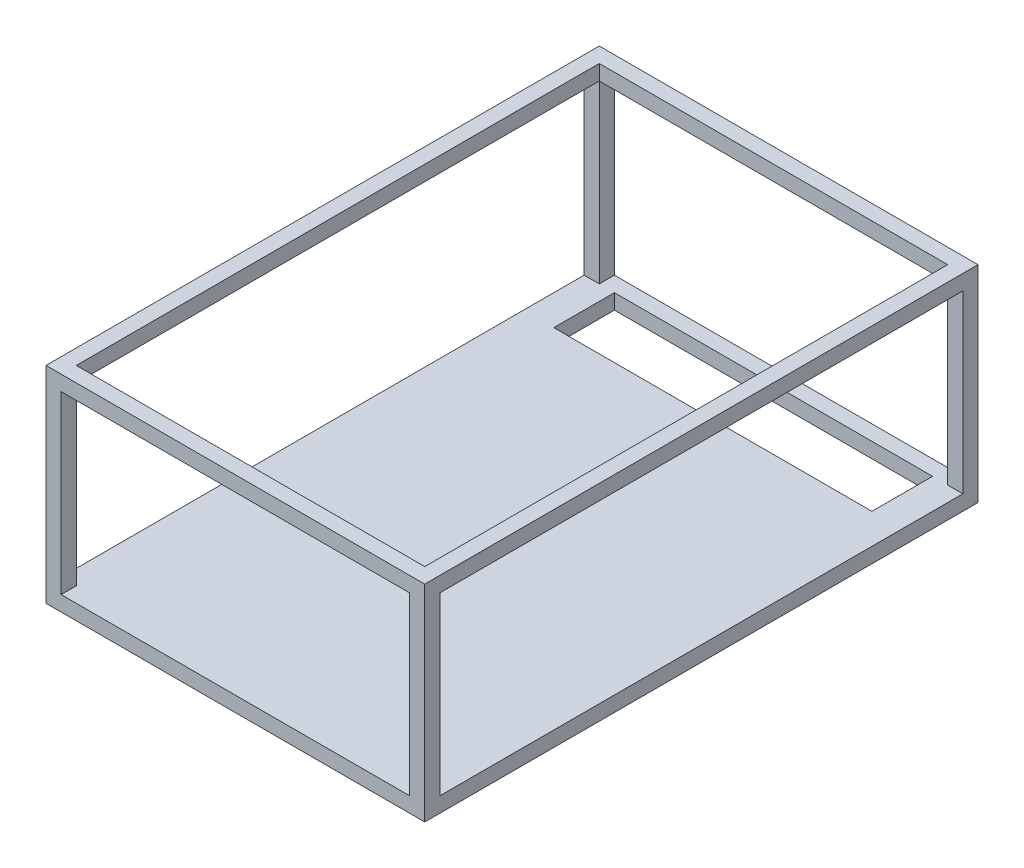
SolidWorks part; units mm, degrees
ref_plane "Ebene vorne" through (0, 0, 0) normal (0, 0, 1) x (1, 0, 0)
ref_plane "Ebene oben" through (0, 0, 0) normal (0, 1, 0) x (1, 0, 0)
ref_plane "Ebene rechts" through (0, 0, 0) normal (1, 0, 0) x (0, 0, -1)
sketch "Sketch1" plane through (0, 0, 0) normal (0, 0, 1) x (1, 0, 0)
  line L1 (-62.5, -34) -> (62.5, -34)
  line L2 (-62.5, -34) -> (-62.5, 34)
  line L3 (-62.5, 34) -> (62.5, 34)
  line L4 (62.5, -34) -> (62.5, 34)
  line L5 (-62.5, -34) -> (62.5, 34) construction
  line L6 (-62.5, 34) -> (62.5, -34) construction
  point P0 (0, 0)
  dimension "D1" = 125
  dimension "D2" = 68
extrude "Boss-Extrude1" add sketch "Sketch1" along normal blind 182.6
sketch "Sketch2" plane through (62.5, 0, 0) normal (1, 0, 0) x (0, 0, -1)
  line L0 (-182.6, 34) -> (0, -34) construction
  line L1 (-182.6, 34) -> (0, 34) construction
  line L2 (-5, -29) -> (-177.6, -29)
  line L3 (-5, -29) -> (-5, 29)
  line L4 (-5, 29) -> (-177.6, 29)
  line L5 (-177.6, -29) -> (-177.6, 29)
  line L6 (-5, -29) -> (-177.6, 29) construction
  line L7 (-5, 29) -> (-177.6, -29) construction
  line L8 (-182.6, -34) -> (-182.6, 34) construction
  point P4 (-91.3, 0)
  dimension "D1" = 5
  dimension "D2" = 5
extrude "Cut-Extrude1" cut sketch "Sketch2" against normal through all
sketch "Sketch3" plane through (0, 0, 0) normal (0, 0, -1) x (-1, 0, 0)
  line L0 (-62.5, 34) -> (62.5, 34) construction
  line L1 (57.5, -29) -> (-57.5, -29)
  line L2 (57.5, -29) -> (57.5, 29)
  line L3 (57.5, 29) -> (-57.5, 29)
  line L4 (-57.5, -29) -> (-57.5, 29)
  line L5 (57.5, -29) -> (-57.5, 29) construction
  line L6 (57.5, 29) -> (-57.5, -29) construction
  line L7 (-62.5, -34) -> (-62.5, 34) construction
  point P0 (0, 0)
  dimension "D1" = 5
  dimension "D2" = 5
extrude "Cut-Extrude2" cut sketch "Sketch3" against normal through all
sketch "Sketch4" plane through (0, 34, 0) normal (0, 1, 0) x (1, 0, 0)
  line L0 (-62.5, 0) -> (62.5, -182.6) construction
  line L1 (62.5, -182.6) -> (62.5, 0) construction
  line L2 (-57.5, -5) -> (57.5, -5)
  line L3 (-57.5, -5) -> (-57.5, -177.6)
  line L4 (-57.5, -177.6) -> (57.5, -177.6)
  line L5 (57.5, -5) -> (57.5, -177.6)
  line L6 (-57.5, -5) -> (57.5, -177.6) construction
  line L7 (-57.5, -177.6) -> (57.5, -5) construction
  line L8 (62.5, 0) -> (-62.5, 0) construction
  point P4 (0, -91.3)
  dimension "D1" = 5
  dimension "D2" = 5
extrude "Cut-Extrude3" cut sketch "Sketch4" against normal blind 63
sketch "Sketch5" plane through (0, -29, 0) normal (0, 1, 0) x (1, 0, 0)
  line L0 (-62.5, -15) -> (62.5, -15) construction
  line L1 (-62.5, -182.6) -> (-62.5, 0) construction
  line L2 (62.5, -182.6) -> (62.5, 0) construction
  line L4 (57.5, -5) -> (-57.5, -5) construction
  line L5 (57.5, -177.6) -> (57.5, -5) construction
  line L6 (-52.5, -25) -> (52.5, -25)
  line L7 (-52.5, -25) -> (-52.5, -5)
  line L8 (-52.5, -5) -> (52.5, -5)
  line L9 (52.5, -25) -> (52.5, -5)
  line L10 (-52.5, -25) -> (52.5, -5) construction
  line L11 (-52.5, -5) -> (52.5, -25) construction
  point P6 (0, -15)
  dimension "D1" = 10
  dimension "D2" = 5
extrude "Cut-Extrude4" cut sketch "Sketch5" against normal through all
